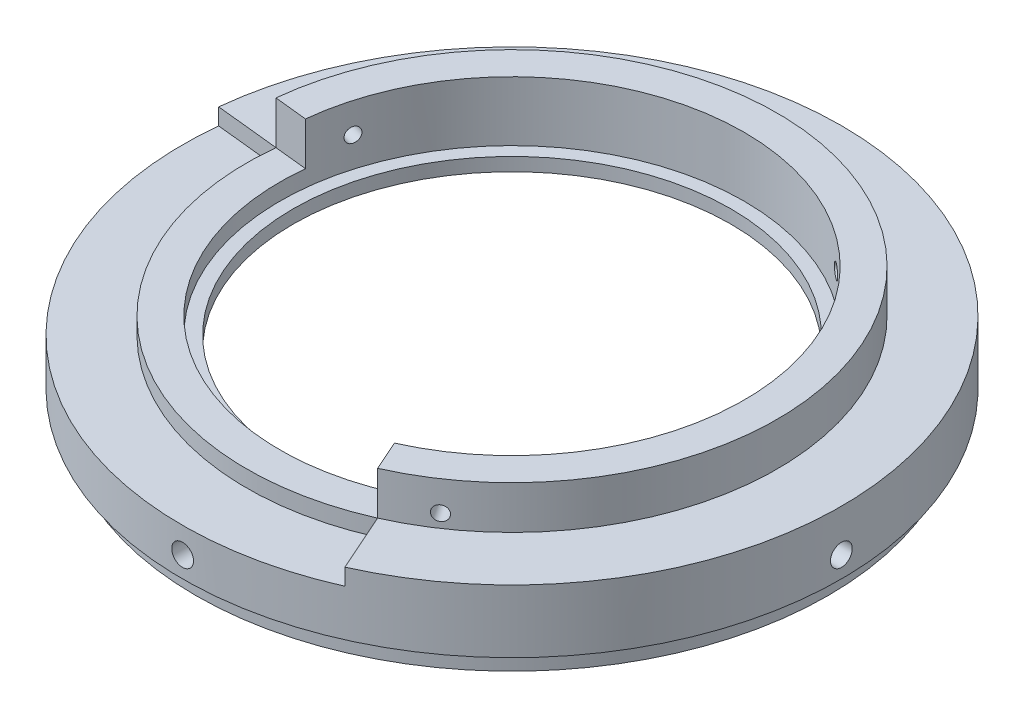
SolidWorks part; units mm, degrees
ref_plane "Front Plane" through (0, 0, 0) normal (0, 0, 1) x (1, 0, 0)
ref_plane "Top Plane" through (0, 0, 0) normal (0, 1, 0) x (1, 0, 0)
ref_plane "Right Plane" through (0, 0, 0) normal (1, 0, 0) x (0, 0, -1)
sketch "Sketch2" plane through (0, 0, 0) normal (0, 0, 1) x (1, 0, 0)
  line L0 (47.675, 0) -> (0, 0) construction
  line L1 (0, 0) -> (0, 12.7) construction
  line L2 (49.7, 12.7) -> (49.7, 3.2004)
  line L3 (49.7, 3.2004) -> (47.675, 3.2004)
  line L4 (47.675, 3.2004) -> (47.675, 0)
  line L5 (0, 12.7) -> (49.7, 12.7) construction
  line L6 (49.7, 12.7) -> (40, 12.7)
  line L11 (40, 12.7) -> (40, 19.2)
  line L12 (40, 19.2) -> (35, 19.2)
  line L13 (35, 19.2) -> (35, 10.2)
  line L14 (35, 10.2) -> (33, 10.2)
  line L15 (33, 10.2) -> (33, 8.2)
  line L16 (33, 8.2) -> (44.7, 0)
  line L17 (44.7, 0) -> (47.675, 0)
  dimension "D1" = 49.7
  dimension "D2" = 2.025
  dimension "D3" = 9.4996
  dimension "D4" = 12.7
  dimension "D5" = 35
  dimension "D6" = 2
  dimension "D7" = 5
  dimension "D8" = 2.5
  dimension "D9" = 5
  dimension "D10" = 9
  dimension "D11" = 2
revolve "Revolve1" add sketch "Sketch2" angle 360 about L1
ref_axis "Axis1" through (0, 13.335, 0) along (0, -1, 0)
sketch "Sketch5" plane through (0, 0, 0) normal (0, 0, 1) x (1, 0, 0)
  line L0 (0, 13.335) -> (0, -0.635) construction
  line L1 (0, 12.7) -> (0, 0) construction
  line L2 (-44.7, 0) -> (44.7, 0) construction
  line L3 (49.7, 12.7) -> (-49.7, 12.7) construction
  circle A0 centre (0, 6.35) radius 1.6425
  point P10 (0, 6.35)
  dimension "D1" = 3.285
extrude "Cut-Extrude1" cut sketch "Sketch5" against normal through all
ref_plane "Plane1" through (0, 0, 0) normal (-0.5878, 0, 0.809) x (0.809, 0, 0.5878)
sketch "Sketch6" plane through (0, 0, 0) normal (-0.5878, 0, 0.809) x (0.809, 0, 0.5878)
  line L0 (0, 19.2) -> (0, 10.2) construction
  line L2 (35, 19.2) -> (-35, 19.2) construction
  line L5 (0, 13.335) -> (0, -0.635) construction
  line L6 (35, 10.2) -> (-35, 10.2) construction
  circle A0 centre (0, 14.7) radius 1.095
  dimension "D1" = 2.19
extrude "Cut-Extrude2" cut sketch "Sketch6" against normal through all
pattern_circular "CirPattern1" count 4 over 360 about axis through (0, 13.335, 0) along (0, -1, 0) of "Cut-Extrude1"
sketch "Sketch7" plane through (0, 19.2, 0) normal (0, 1, 0) x (-1, 0, 0)
  line L0 (39.7809, -4.1811) -> (34.8083, -3.6585)
  line L1 (-16.2695, 36.5418) -> (-14.2358, 31.9741)
  line L2 (0, 0) -> (23.5114, 32.3607) construction
  line L3 (6.2161, -4.5162) -> (-6.2161, 4.5162) construction
  arc A0 (34.8083, -3.6585) -> (-14.2358, 31.9741) centre (0, 0) ccw
  circle A1 centre (0, 0) radius 35 construction
  arc A2 (-16.2695, 36.5418) -> (39.7809, -4.1811) centre (0, 0) cw
  circle A3 centre (0, 0) radius 40 construction
  dimension "D1" = 120
extrude "Cut-Extrude3" cut sketch "Sketch7" against normal up to surface (6.5 mm away) up to face at (0, 12.7, -40)
sketch "Sketch8" plane through (0, 12.7, 0) normal (0, 1, 0) x (1, 0, 0)
  line L0 (-49.4277, 5.1951) -> (-39.7809, 4.1811)
  line L1 (16.2695, -36.5418) -> (20.2148, -45.4032)
  line L2 (16.2695, -36.5418) -> (14.2358, -31.9741) construction
  line L3 (-34.8083, 3.6585) -> (-39.7809, 4.1811) construction
  arc A0 (-39.7809, 4.1811) -> (16.2695, -36.5418) centre (0, 0) ccw
  arc A1 (16.2695, -36.5418) -> (-39.7809, 4.1811) centre (0, 0) ccw construction
  arc A2 (20.2148, -45.4032) -> (-49.4277, 5.1951) centre (0, 0) cw
  circle A3 centre (0, 0) radius 49.7 construction
extrude "Cut-Extrude4" cut sketch "Sketch8" against normal up to surface (2.5 mm away) up to face at (0, 10.2, -33)
pattern_circular "CirPattern2" count 2 every 110 about axis through (0, 13.335, 0) along (0, -1, 0) of "Cut-Extrude2"
pattern_circular "CirPattern3" count 2 every 110 about axis through (0, 13.335, 0) along (0, -1, 0) of "Cut-Extrude2"
